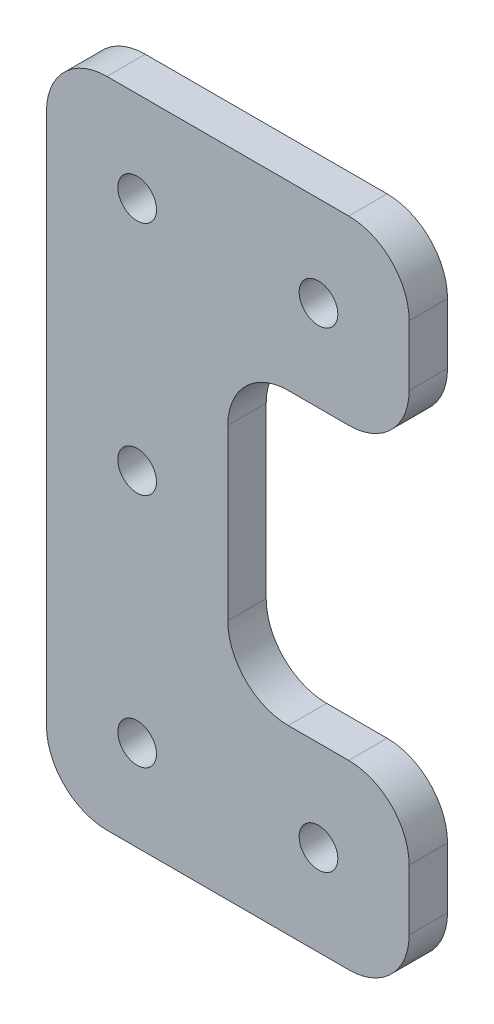
SolidWorks part; units mm, degrees
ref_plane "Front Plane" through (0, 0, 0) normal (0, 0, 1) x (1, 0, 0)
ref_plane "Top Plane" through (0, 0, 0) normal (0, 1, 0) x (1, 0, 0)
ref_plane "Right Plane" through (0, 0, 0) normal (1, 0, 0) x (0, 0, -1)
sketch "Sketch1" plane through (0, 0, 0) normal (0, 0, 1) x (1, 0, 0)
  line L2 (0, 54) -> (0, 0)
  line L3 (15, 15) -> (30, 15)
  line L4 (15, 39) -> (15, 15)
  line L7 (0, 0) -> (30, 0)
  line L8 (30, 15) -> (30, 0)
  line L11 (15, 39) -> (30, 39)
  line L13 (30, 39) -> (30, 54)
  line L14 (0, 54) -> (30, 54)
  dimension "D1" = 15
  dimension "D2" = 30
  dimension "D3" = 24
  dimension "D4" = 15
  dimension "D5" = 30
  dimension "D6" = 15
extrude "Boss-Extrude1" add sketch "Sketch1" along normal blind 3.175
fillet "Fillet1" radius 5 8 edges at (30, 0, 1.5875) (30, 15, 1.5875) (15, 15, 1.5875) (0, 0, 1.5875) (0, 54, 1.5875) (30, 54, 1.5875) (30, 39, 1.5875) (15, 39, 1.5875)
sketch "Sketch2" plane through (0, 0, 3.175) normal (0, 0, 1) x (1, 0, 0)
  line L0 (30, 7.5) -> (0, 7.5) construction
  line L3 (30, 5) -> (30, 10) construction
  line L6 (0, 49) -> (0, 5) construction
  line L7 (30, 46.5) -> (0, 46.5) construction
  line L9 (30, 44) -> (30, 49) construction
  line L10 (7.5, 0) -> (7.5, 54) construction
  line L11 (5, 0) -> (25, 0) construction
  line L12 (25, 54) -> (5, 54) construction
  circle A0 centre (7.5, 7.5) radius 1.6
  circle A1 centre (7.5, 46.5) radius 1.6
  circle A2 centre (22.5, 7.5) radius 1.6
  circle A3 centre (7.5, 27) radius 1.6
  circle A4 centre (22.5, 46.5) radius 1.6
  dimension "D1" = 3.2
  dimension "D2" = 7.5
  dimension "D3" = 15
extrude "Cut-Extrude1" cut sketch "Sketch2" against normal through all
